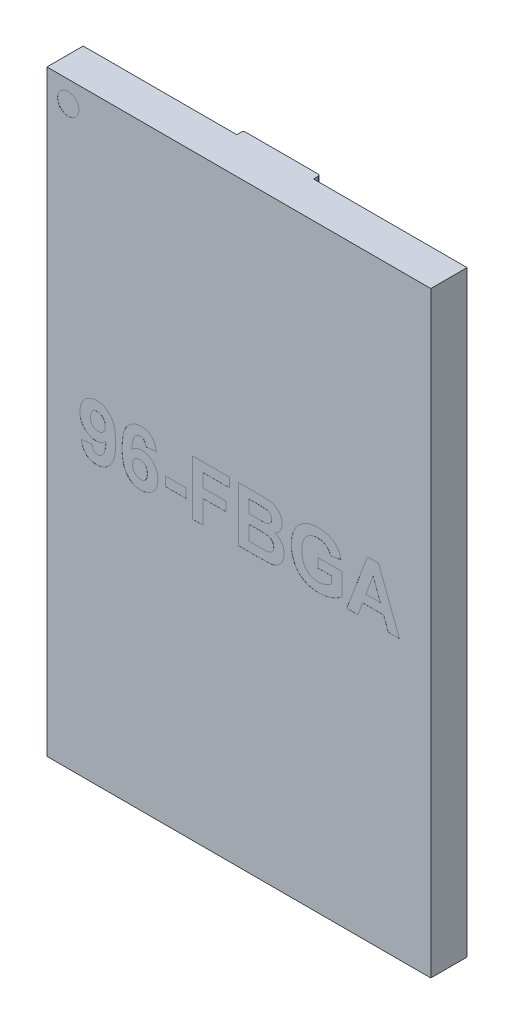
SolidWorks part; units mm, degrees
ref_plane "Front Plane" through (0, 0, 0) normal (0, 0, 1) x (1, 0, 0)
ref_plane "Top Plane" through (0, 0, 0) normal (0, 1, 0) x (1, 0, 0)
ref_plane "Right Plane" through (0, 0, 0) normal (1, 0, 0) x (0, 0, -1)
sketch "Sketch1" plane through (0, 0, 0) normal (0, 0, 1) x (1, 0, 0)
  line L1 (-4.5, -7) -> (4.5, -7)
  line L2 (-4.5, -7) -> (-4.5, 7)
  line L3 (-4.5, 7) -> (4.5, 7)
  line L4 (4.5, -7) -> (4.5, 7)
  line L5 (-4.5, -7) -> (4.5, 7) construction
  line L6 (-4.5, 7) -> (4.5, -7) construction
  point P0 (0, 0)
  dimension "D1" = 9
  dimension "D2" = 14
extrude "Boss-Extrude1" add sketch "Sketch1" along normal blind 0.85
sketch "Sketch2" plane through (0, 0, 0) normal (0, 0, -1) x (-1, 0, 0)
  line L0 (0, 7) -> (0, -7.6495) construction
  line L1 (-4.5, 7) -> (4.5, 7) construction
  line L2 (4.5, -7) -> (-4.5, -7) construction
  line L3 (-0.9, 7) -> (0.9, 7)
  line L4 (-0.9, 7) -> (-0.9, -7)
  line L5 (-0.9, -7) -> (0.9, -7)
  line L6 (0.9, 7) -> (0.9, -7)
  dimension "D1" = 1.8
  dimension "D2" = 0.9
extrude "Boss-Extrude2" add sketch "Sketch2" along normal blind 0.155
sketch "Sketch3" plane through (0, 0, 0) normal (0, 0, -1) x (-1, 0, 0)
  line L0 (-4.5, 7) -> (-0.9, 7) construction
  line L1 (0, 7) -> (0, -7.6097) construction
  line L2 (0.9, 7) -> (-0.9, 7) construction
  circle A0 centre (-3.2, 6) radius 0.225
  circle A1 centre (-2.4, 6) radius 0.225
  circle A2 centre (-1.6, 6) radius 0.225
  circle A3 centre (-3.2, 5.2) radius 0.225
  circle A4 centre (-2.4, 5.2) radius 0.225
  circle A5 centre (-1.6, 5.2) radius 0.225
  circle A6 centre (-3.2, 4.4) radius 0.225
  circle A7 centre (-2.4, 4.4) radius 0.225
  circle A8 centre (-1.6, 4.4) radius 0.225
  circle A9 centre (-3.2, 3.6) radius 0.225
  circle A10 centre (-2.4, 3.6) radius 0.225
  circle A11 centre (-1.6, 3.6) radius 0.225
  circle A12 centre (-3.2, 2.8) radius 0.225
  circle A13 centre (-2.4, 2.8) radius 0.225
  circle A14 centre (-1.6, 2.8) radius 0.225
  circle A15 centre (-3.2, 2) radius 0.225
  circle A16 centre (-2.4, 2) radius 0.225
  circle A17 centre (-1.6, 2) radius 0.225
  circle A18 centre (-3.2, 1.2) radius 0.225
  circle A19 centre (-2.4, 1.2) radius 0.225
  circle A20 centre (-1.6, 1.2) radius 0.225
  circle A21 centre (-3.2, 0.4) radius 0.225
  circle A22 centre (-2.4, 0.4) radius 0.225
  circle A23 centre (-1.6, 0.4) radius 0.225
  circle A24 centre (-3.2, -0.4) radius 0.225
  circle A25 centre (-2.4, -0.4) radius 0.225
  circle A26 centre (-1.6, -0.4) radius 0.225
  circle A27 centre (-3.2, -1.2) radius 0.225
  circle A28 centre (-2.4, -1.2) radius 0.225
  circle A29 centre (-1.6, -1.2) radius 0.225
  circle A30 centre (-3.2, -2) radius 0.225
  circle A31 centre (-2.4, -2) radius 0.225
  circle A32 centre (-1.6, -2) radius 0.225
  circle A33 centre (-3.2, -2.8) radius 0.225
  circle A34 centre (-2.4, -2.8) radius 0.225
  circle A35 centre (-1.6, -2.8) radius 0.225
  circle A36 centre (-3.2, -3.6) radius 0.225
  circle A37 centre (-2.4, -3.6) radius 0.225
  circle A38 centre (-1.6, -3.6) radius 0.225
  circle A39 centre (-3.2, -4.4) radius 0.225
  circle A40 centre (-2.4, -4.4) radius 0.225
  circle A41 centre (-1.6, -4.4) radius 0.225
  circle A42 centre (-3.2, -5.2) radius 0.225
  circle A43 centre (-2.4, -5.2) radius 0.225
  circle A44 centre (-1.6, -5.2) radius 0.225
  circle A45 centre (-3.2, -6) radius 0.225
  circle A46 centre (-2.4, -6) radius 0.225
  circle A47 centre (-1.6, -6) radius 0.225
  circle A48 centre (1.6, -6) radius 0.225
  circle A49 centre (2.4, -6) radius 0.225
  circle A50 centre (3.2, -6) radius 0.225
  circle A51 centre (1.6, -5.2) radius 0.225
  circle A52 centre (2.4, -5.2) radius 0.225
  circle A53 centre (3.2, -5.2) radius 0.225
  circle A54 centre (1.6, -4.4) radius 0.225
  circle A55 centre (2.4, -4.4) radius 0.225
  circle A56 centre (3.2, -4.4) radius 0.225
  circle A57 centre (1.6, -3.6) radius 0.225
  circle A58 centre (2.4, -3.6) radius 0.225
  circle A59 centre (3.2, -3.6) radius 0.225
  circle A60 centre (1.6, -2.8) radius 0.225
  circle A61 centre (2.4, -2.8) radius 0.225
  circle A62 centre (3.2, -2.8) radius 0.225
  circle A63 centre (1.6, -2) radius 0.225
  circle A64 centre (2.4, -2) radius 0.225
  circle A65 centre (3.2, -2) radius 0.225
  circle A66 centre (1.6, -1.2) radius 0.225
  circle A67 centre (2.4, -1.2) radius 0.225
  circle A68 centre (3.2, -1.2) radius 0.225
  circle A69 centre (1.6, -0.4) radius 0.225
  circle A70 centre (2.4, -0.4) radius 0.225
  circle A71 centre (3.2, -0.4) radius 0.225
  circle A72 centre (1.6, 0.4) radius 0.225
  circle A73 centre (2.4, 0.4) radius 0.225
  circle A74 centre (3.2, 0.4) radius 0.225
  circle A75 centre (1.6, 1.2) radius 0.225
  circle A76 centre (2.4, 1.2) radius 0.225
  circle A77 centre (3.2, 1.2) radius 0.225
  circle A78 centre (1.6, 2) radius 0.225
  circle A79 centre (2.4, 2) radius 0.225
  circle A80 centre (3.2, 2) radius 0.225
  circle A81 centre (1.6, 2.8) radius 0.225
  circle A82 centre (2.4, 2.8) radius 0.225
  circle A83 centre (3.2, 2.8) radius 0.225
  circle A84 centre (1.6, 3.6) radius 0.225
  circle A85 centre (2.4, 3.6) radius 0.225
  circle A86 centre (3.2, 3.6) radius 0.225
  circle A87 centre (1.6, 4.4) radius 0.225
  circle A88 centre (2.4, 4.4) radius 0.225
  circle A89 centre (3.2, 4.4) radius 0.225
  circle A90 centre (1.6, 5.2) radius 0.225
  circle A91 centre (2.4, 5.2) radius 0.225
  circle A92 centre (3.2, 5.2) radius 0.225
  circle A93 centre (1.6, 6) radius 0.225
  circle A94 centre (2.4, 6) radius 0.225
  circle A95 centre (3.2, 6) radius 0.225
  dimension "D1" = 1
  dimension "D2" = 3
  dimension "D3" = 16
extrude "Boss-Extrude3" add sketch "Sketch3" along normal blind 0.25
fillet "Fillet1" radius 0.05 2 edges at (-0.9, 0, -0.155) (0.9, 0, -0.155)
fillet "Fillet3" radius 0.225 96 edges at (-2.975, 6, -0.25) (-2.175, 6, -0.25) (-1.375, 6, -0.25) (-2.975, 5.2, -0.25) (-2.175, 5.2, -0.25) (-1.375, 5.2, -0.25) (-2.975, 4.4, -0.25) (-2.175, 4.4, -0.25) (-1.375, 4.4, -0.25) (-2.975, 3.6, -0.25) (-2.175, 3.6, -0.25) (-1.375, 3.6, -0.25) (-2.975, 2.8, -0.25) (-2.175, 2.8, -0.25) (-1.375, 2.8, -0.25) (-2.975, 2, -0.25) (-2.175, 2, -0.25) (-1.375, 2, -0.25) (-2.975, 1.2, -0.25) (-2.175, 1.2, -0.25) (-1.375, 1.2, -0.25) (-2.975, 0.4, -0.25) (-2.175, 0.4, -0.25) (-1.375, 0.4, -0.25) (-2.975, -0.4, -0.25) (-2.175, -0.4, -0.25) (-1.375, -0.4, -0.25) (-2.975, -1.2, -0.25) (-2.175, -1.2, -0.25) (-1.375, -1.2, -0.25) (-2.975, -2, -0.25) (-2.175, -2, -0.25) (-1.375, -2, -0.25) (-2.975, -2.8, -0.25) (-2.175, -2.8, -0.25) (-1.375, -2.8, -0.25) (-2.975, -3.6, -0.25) (-2.175, -3.6, -0.25) (-1.375, -3.6, -0.25) (-2.975, -4.4, -0.25) (-2.175, -4.4, -0.25) (-1.375, -4.4, -0.25) (-2.975, -5.2, -0.25) (-2.175, -5.2, -0.25) (-1.375, -5.2, -0.25) (-2.975, -6, -0.25) (-2.175, -6, -0.25) (1.375, -6, -0.25) (2.175, -6, -0.25) (2.975, -6, -0.25) (1.375, -5.2, -0.25) (2.175, -5.2, -0.25) (2.975, -5.2, -0.25) (1.375, -4.4, -0.25) (2.175, -4.4, -0.25) (2.975, -4.4, -0.25) (1.375, -3.6, -0.25) (2.175, -3.6, -0.25) (2.975, -3.6, -0.25) (1.375, -2.8, -0.25) (2.175, -2.8, -0.25) (2.975, -2.8, -0.25) (1.375, -2, -0.25) (2.175, -2, -0.25) (2.975, -2, -0.25) (1.375, -1.2, -0.25) (2.175, -1.2, -0.25) (2.975, -1.2, -0.25) (1.375, -0.4, -0.25) (2.175, -0.4, -0.25) (2.975, -0.4, -0.25) (1.375, 0.4, -0.25) (2.175, 0.4, -0.25) (2.975, 0.4, -0.25) (1.375, 1.2, -0.25) (2.175, 1.2, -0.25) (2.975, 1.2, -0.25) (1.375, 2, -0.25) (2.175, 2, -0.25) (2.975, 2, -0.25) (1.375, 2.8, -0.25) (2.175, 2.8, -0.25) (2.975, 2.8, -0.25) (1.375, 3.6, -0.25) (2.175, 3.6, -0.25) (2.975, 3.6, -0.25) (1.375, 4.4, -0.25) (2.175, 4.4, -0.25) (2.975, 4.4, -0.25) (1.375, 5.2, -0.25) (2.175, 5.2, -0.25) (2.975, 5.2, -0.25) (1.375, 6, -0.25) (2.175, 6, -0.25) (-1.375, -6, -0.25) (2.975, 6, -0.25)
sketch "Sketch4" plane through (0, 0, 0.85) normal (0, 0, 1) x (1, 0, 0)
  circle A0 centre (-4, 6.5) radius 0.25
extrude "Cut-Extrude1" cut sketch "Sketch4" against normal blind 0.001
sketch "Sketch6" plane through (0, 0, 0.85) normal (0, 0, 1) x (1, 0, 0)
  text T0 "96-FBGA" font "Arial" height in points 5
extrude "Cut-Extrude2" cut sketch "Sketch6" against normal blind 0.001
